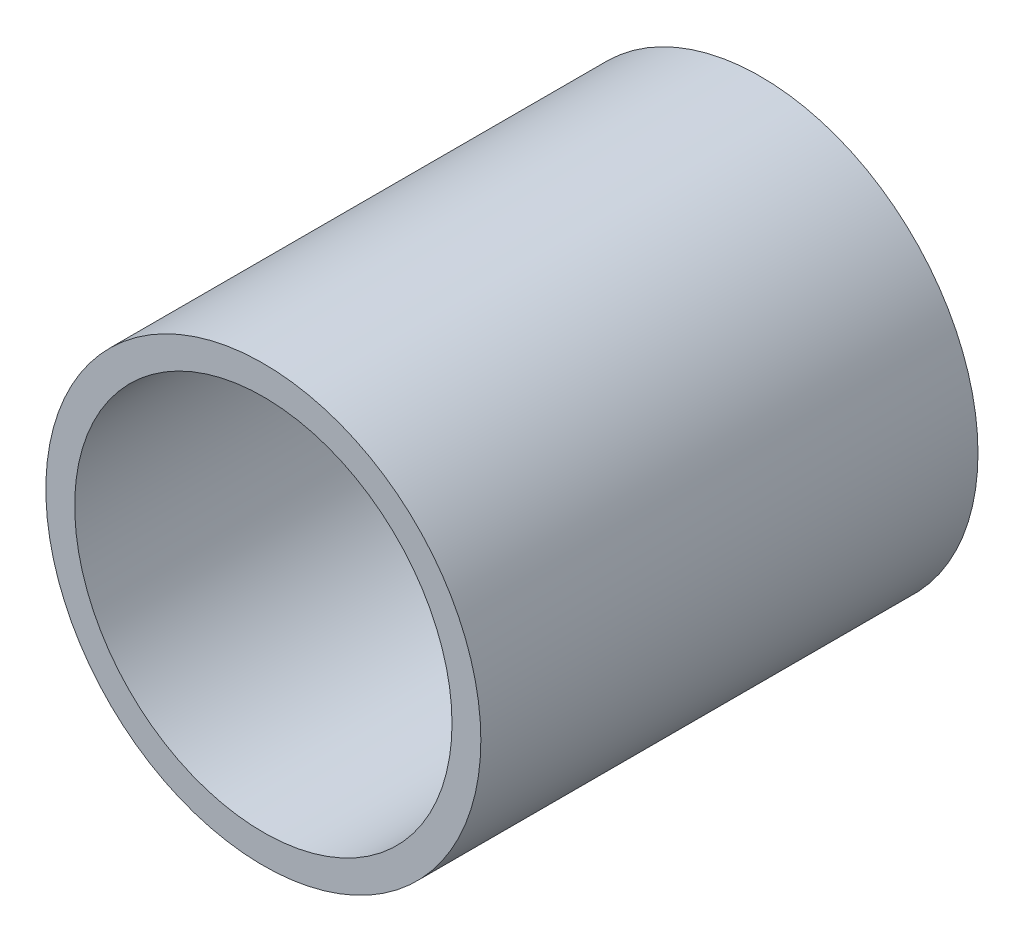
SolidWorks part; units mm, degrees
material "Alloy Steel"
ref_plane "Front Plane" through (0, 0, 0) normal (0, 0, 1) x (1, 0, 0)
ref_plane "Top Plane" through (0, 0, 0) normal (0, 1, 0) x (1, 0, 0)
ref_plane "Right Plane" through (0, 0, 0) normal (1, 0, 0) x (0, 0, -1)
sketch "Sketch1" plane through (0, 0, 0) normal (0, 0, 1) x (1, 0, 0)
  line L0 (-11.1125, 0) -> (11.1125, 0) construction
  line L1 (0, -11.1125) -> (0, 11.1125) construction
  circle A0 centre (0, 0) radius 11.1125
  circle A1 centre (0, 0) radius 9.6393
  point P4 (0, 0)
  point P9 (0, 0)
  point P10 (9.6393, 0)
  dimension "ID" = 19.2786
  dimension "OD" = 22.225
  dimension "Wall Thickness" = 1.4732
sketch "Sketch2" plane through (0, 0, 0) normal (1, 0, 0) x (0, 0, -1)
  line L0 (12.7, 11.1125) -> (-12.7, 11.1125) construction
  line L1 (0, 11.1125) -> (0, -11.1125) construction
  point P3 (12.8588, 11.1125)
  point P4 (0, 11.1125)
  point P5 (-12.8588, 11.1125)
  dimension "Length" = 25.4
  dimension "D1" = 25.5587
  dimension "D2" = 25.5587
sketch "Sketch3" plane through (0, 0, 0) normal (0, 0, 1) x (1, 0, 0)
  line L0 (0, -11.1125) -> (0, 11.1125) construction
  circle A0 centre (0, 0) radius 11.1125
  circle A1 centre (0, 0) radius 9.6393
  circle A2 centre (0, 0) radius 9.6393 construction
extrude "Boss-Extrude1" add sketch "Sketch3" along normal mid plane 25.4
equation "\"D1@Boss-Extrude1\" = \"Length@Sketch2\""
equation "\"D1@Sketch2\"=\"OD@Sketch1\"*1.15"
equation "\"D2@Sketch2\"=\"D1@Sketch2\""
